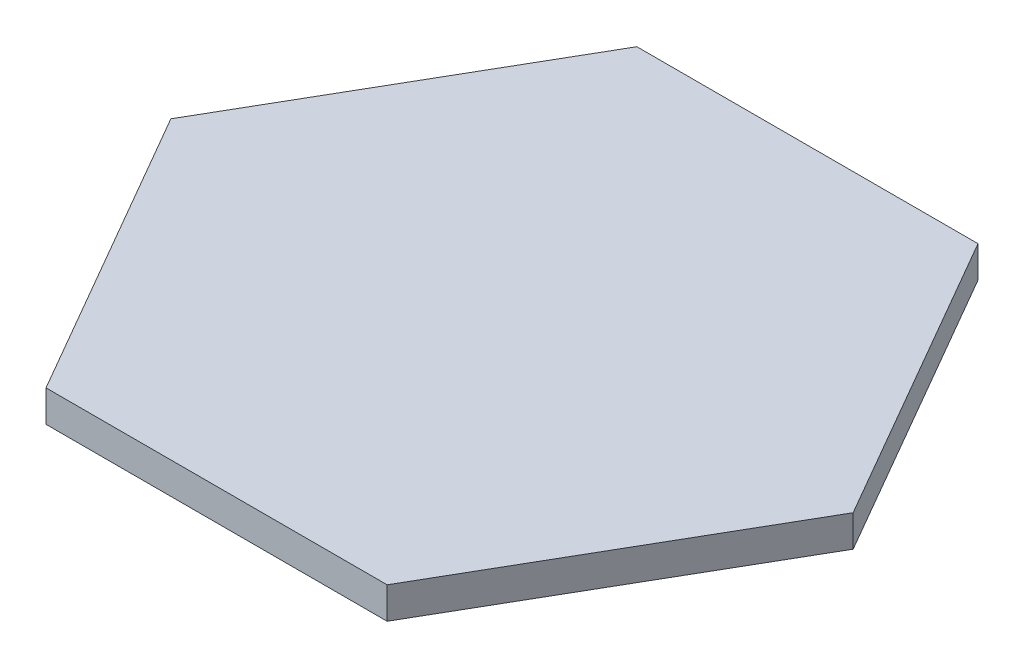
SolidWorks part; units mm, degrees
ref_plane "Front Plane" through (0, 0, 0) normal (0, 0, 1) x (1, 0, 0)
ref_plane "Top Plane" through (0, 0, 0) normal (0, 1, 0) x (1, 0, 0)
ref_plane "Right Plane" through (0, 0, 0) normal (1, 0, 0) x (0, 0, -1)
sketch "Sketch1" plane through (0, 0, 0) normal (0, 1, 0) x (1, 0, 0)
  line L1 (-5.3982, -9.35) -> (5.3982, -9.35)
  line L2 (5.3982, -9.35) -> (10.7965, 0)
  line L3 (10.7965, 0) -> (5.3982, 9.35)
  line L4 (5.3982, 9.35) -> (-5.3982, 9.35)
  line L5 (-5.3982, 9.35) -> (-10.7965, 0)
  line L6 (-10.7965, 0) -> (-5.3982, -9.35)
  circle A0 centre (0, 0) radius 9.35 construction
  dimension "D1" = 18.7
extrude "Boss-Extrude1" add sketch "Sketch1" along normal blind 1
